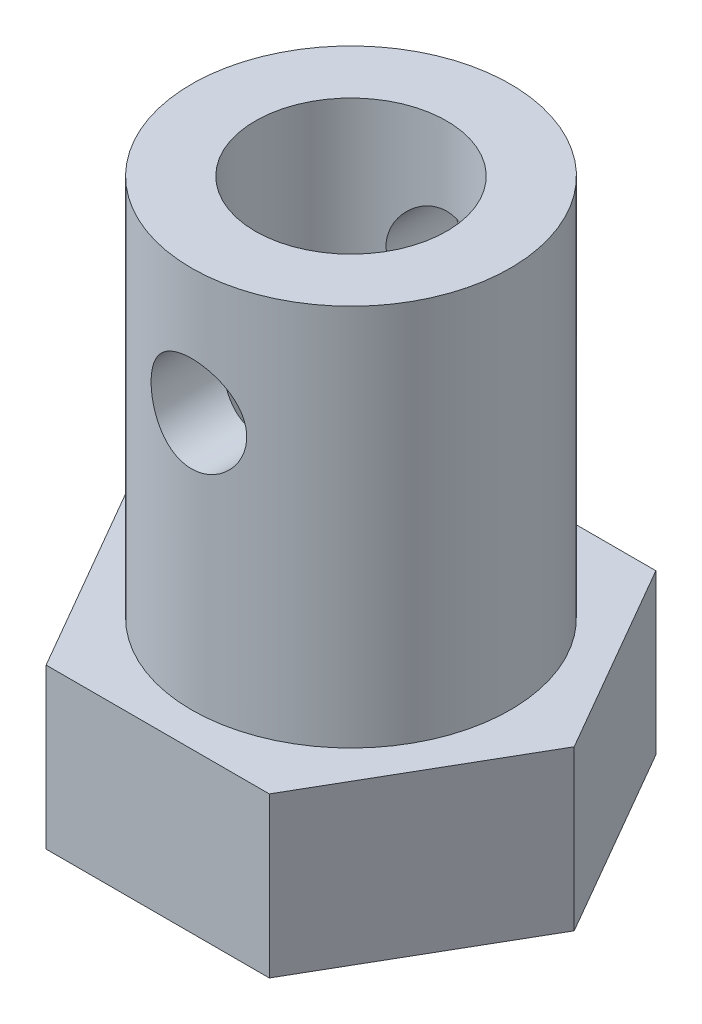
SolidWorks part; units mm, degrees
ref_plane "前视基准面" through (0, 0, 0) normal (0, 0, 1) x (1, 0, 0)
ref_plane "上视基准面" through (0, 0, 0) normal (0, 1, 0) x (1, 0, 0)
ref_plane "右视基准面" through (0, 0, 0) normal (1, 0, 0) x (0, 0, -1)
sketch "草图1" plane through (0, 0, 0) normal (0, 1, 0) x (1, 0, 0)
  line L1 (-7, 0) -> (-3.5, -6.0622)
  line L2 (-3.5, -6.0622) -> (3.5, -6.0622)
  line L3 (3.5, -6.0622) -> (7, 0)
  line L4 (7, 0) -> (3.5, 6.0622)
  line L5 (3.5, 6.0622) -> (-3.5, 6.0622)
  line L6 (-3.5, 6.0622) -> (-7, 0)
  circle A0 centre (0, 0) radius 6.0622 construction
  point P1 (0, 0)
  point P10 (0, 0)
  point P11 (0, 0)
extrude "凸台-拉伸1" add sketch "草图1" along normal blind 5
sketch "草图3" plane through (0, 0, 0) normal (0, 1, 0) x (1, 0, 0)
  circle A0 centre (0, 0) radius 5
extrude "凸台-拉伸2" add sketch "草图3" along normal blind 17
sketch "草图4" plane through (0, 0, 0) normal (0, 1, 0) x (1, 0, 0)
  circle A0 centre (0, 0) radius 3
extrude "切除-拉伸1" cut sketch "草图4" along normal blind 17
sketch "草图5" plane through (0, 0, 0) normal (1, 0, 0) x (0, 0, -1)
sketch "草图6" plane through (0, 0, 0) normal (0, 0, 1) x (1, 0, 0)
  circle A0 centre (0, 13.0475) radius 1.5
extrude "切除-拉伸2" cut sketch "草图6" against normal blind 5 and the other way blind 5
